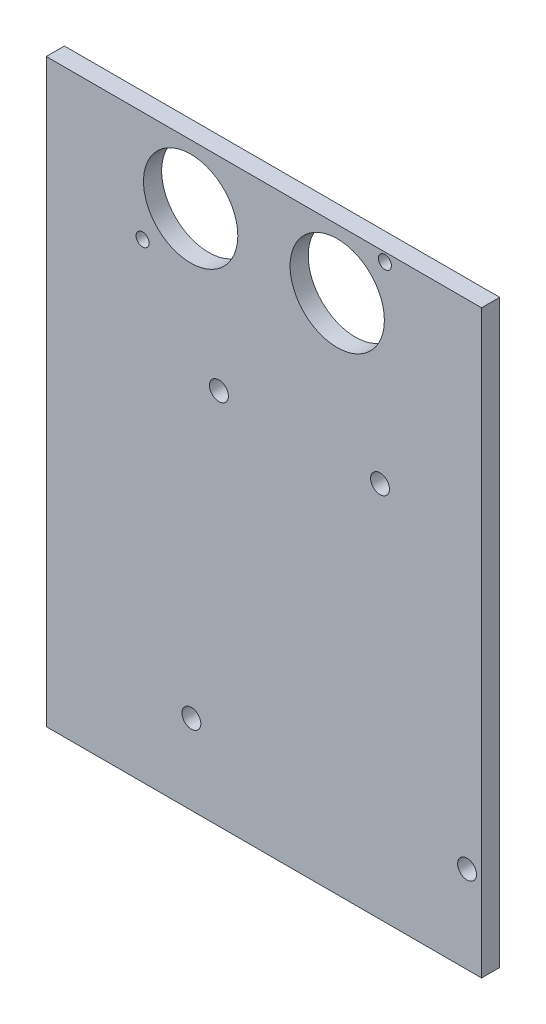
SolidWorks part; units mm, degrees
ref_plane "Front Plane" through (0, 0, 0) normal (0, 0, 1) x (1, 0, 0)
ref_plane "Top Plane" through (0, 0, 0) normal (0, 1, 0) x (1, 0, 0)
ref_plane "Right Plane" through (0, 0, 0) normal (1, 0, 0) x (0, 0, -1)
sketch "Sketch2" plane through (0, 0, 0) normal (0, 0, 1) x (1, 0, 0)
  line L1 (0, 0) -> (76.2, 0)
  line L2 (0, 0) -> (0, 101.6)
  line L3 (0, 101.6) -> (76.2, 101.6)
  line L4 (76.2, 0) -> (76.2, 101.6)
  line L5 (0, 0) -> (76.2, 101.6) construction
  line L6 (0, 101.6) -> (76.2, 0) construction
  point P4 (38.1, 50.8)
  dimension "D1" = 76.2
  dimension "D2" = 101.6
extrude "Boss-Extrude1" add sketch "Sketch2" along normal blind 3.175
sketch "Sketch3" plane through (0, 0, 3.175) normal (0, 0, 1) x (1, 0, 0)
  line L0 (38.1, 101.6) -> (38.1, 91.186) construction
  line L1 (76.2, 101.6) -> (0, 101.6) construction
  line L2 (50.927, 91.186) -> (25.273, 91.186) construction
  line L3 (15.5815, 101.6) -> (60.7935, 101.6) construction
  line L4 (60.7935, 101.6) -> (60.7935, 100.076) construction
  line L5 (60.7935, 100.076) -> (59.2695, 100.076) construction
  line L6 (15.5815, 80.772) -> (60.7935, 80.772) construction
  line L7 (15.5815, 80.772) -> (15.5815, 82.296) construction
  line L8 (15.5815, 82.296) -> (16.8515, 82.296) construction
  line L9 (60.7935, 100.076) -> (60.7935, 80.772) construction
  circle A0 centre (25.273, 91.186) radius 8.255
  circle A1 centre (50.927, 91.186) radius 8.255
  circle A2 centre (59.2695, 100.076) radius 1.143
  circle A3 centre (16.8515, 82.296) radius 1.143
  point P7 (38.1, 91.186)
  point P12 (38.1875, 101.6)
  point P18 (38.1, 91.186)
  dimension "D3" = 16.51
  dimension "D5" = 2.286
  dimension "D6" = 2.286
  dimension "D7" = 1.27
  dimension "D1" = 10.414
  dimension "D2" = 25.654
  dimension "D4" = 45.212
  dimension "D8" = 1.524
extrude "Cut-Extrude1" cut sketch "Sketch3" against normal blind 3.175
sketch "Sketch6" plane through (0, 0, 0) normal (0, 0, -1) x (-1, 0, 0)
  line L0 (-76.2, 0) -> (-76.2, 15.24) construction
  line L1 (-76.2, 15.24) -> (-73.66, 15.24) construction
  line L2 (-73.66, 15.24) -> (-25.4, 15.24) construction
  line L3 (-25.4, 15.24) -> (-25.4, 13.97) construction
  line L4 (-25.4, 13.97) -> (-25.4, 66.04) construction
  line L5 (-25.4, 66.04) -> (-30.226, 66.04) construction
  line L6 (-30.226, 66.04) -> (-58.42, 66.04) construction
  circle A0 centre (-73.66, 15.24) radius 1.651
  circle A1 centre (-25.4, 13.97) radius 1.651
  circle A2 centre (-25.273, 91.186) radius 8.255 construction
  circle A3 centre (-30.226, 66.04) radius 1.651
  circle A4 centre (-58.42, 66.04) radius 1.651
  dimension "D1" = 3.302
  dimension "D4" = 28.194
  dimension "D2" = 15.24
  dimension "D3" = 2.54
  dimension "D5" = 48.26
  dimension "D6" = 1.27
  dimension "D7" = 52.07
  dimension "D8" = 4.826
extrude "Cut-Extrude2" cut sketch "Sketch6" against normal blind 3.175
